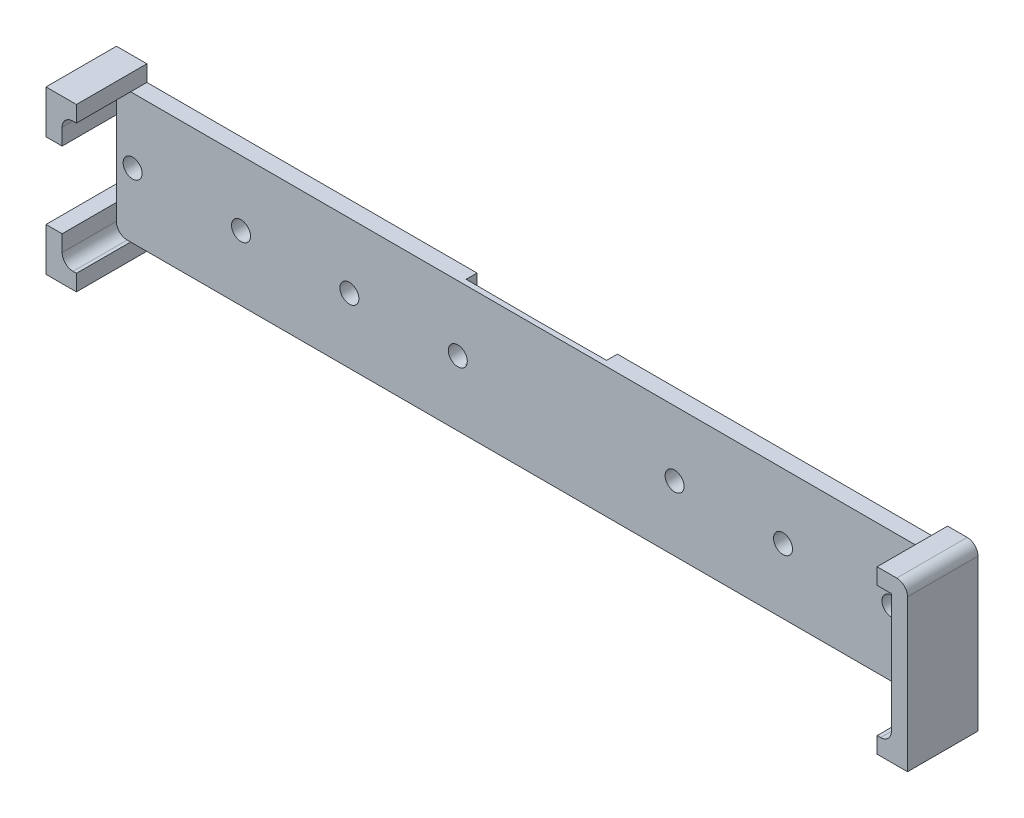
SolidWorks part; units mm, degrees
ref_plane "Front Plane" through (0, 0, 0) normal (0, 0, 1) x (1, 0, 0)
ref_plane "Top Plane" through (0, 0, 0) normal (0, 1, 0) x (1, 0, 0)
ref_plane "Right Plane" through (0, 0, 0) normal (1, 0, 0) x (0, 0, -1)
sketch "Sketch1" plane through (0, 0, 0) normal (0, 0, 1) x (1, 0, 0)
  line L0 (-76.5, 43.2955) -> (-76.5, -49956.7045) construction
  line L1 (-76.5, -12) -> (76.5, -12)
  line L2 (-76.5, -12) -> (-76.5, 12)
  line L3 (-76.5, 12) -> (76.5, 12)
  line L4 (76.5, -12) -> (76.5, 12)
  line L5 (-76.5, -12) -> (76.5, 12) construction
  line L6 (-76.5, 12) -> (76.5, -12) construction
  line L7 (76.5, 42.716) -> (76.5, 17.6033) construction
  point P0 (0, 0)
  dimension "D1" = 153
  dimension "D2" = 24
extrude "Boss-Extrude1" add sketch "Sketch1" along normal blind 3
sketch "Sketch3" plane through (0, 0, 3) normal (0, 0, 1) x (1, 0, 0)
  line L5 (-64.5, 0) -> (938.7663, 0) construction
  line L7 (-79.4776, -9.3658) -> (-79.4776, -12.3658)
  line L8 (-76.5, -9.3658) -> (-76.5, -12)
  line L9 (-70.1258, -5.6258) -> (-82.5217, -18.0217) construction
  line L10 (-76.5, -12) -> (76.5, -12) construction
  line L11 (-73.8658, 14.9776) -> (-73.8658, 12)
  line L12 (-73.8658, -14.9776) -> (-73.8658, -12)
  line L13 (-73.8658, -14.9776) -> (-76.8658, -14.9776)
  line L15 (-73.8658, -12) -> (-76.5, -12)
  line L16 (-79.4776, -12.3658) -> (-79.4776, -14.9776)
  line L17 (-79.4776, -14.9776) -> (-76.8658, -14.9776)
  line L18 (-73.8658, 12) -> (-76.5, 12)
  line L19 (-76.5, 9.3658) -> (-76.5, 12)
  line L21 (-79.4776, 9.3658) -> (-79.4776, 12.3658)
  line L22 (-79.4776, 12.3658) -> (-79.4776, 14.9776)
  line L23 (-79.4776, 14.9776) -> (-76.8658, 14.9776)
  line L24 (-73.8658, 14.9776) -> (-76.8658, 14.9776)
  line L25 (0, 104.9729) -> (0, -49895.0271) construction
  line L42 (-79.4776, 9.3658) -> (-79.4776, 7)
  line L43 (-76.5, 9.3658) -> (-76.5, 7)
  line L44 (-76.5, 12) -> (-76.5, -12) construction
  line L45 (-79.4776, 7) -> (-76.5, 7)
  line L46 (-79.4776, -7) -> (-76.5, -7)
  line L47 (-79.4776, -7) -> (-79.4776, -9.3658)
  line L48 (79.4776, 9.3658) -> (79.4776, -9.3658)
  line L49 (79.4776, -9.3658) -> (79.4776, -12.3658)
  line L50 (79.4776, -12.3658) -> (79.4776, -14.9776)
  line L51 (79.4776, -14.9776) -> (76.8658, -14.9776)
  line L52 (73.8658, -14.9776) -> (76.8658, -14.9776)
  line L53 (73.8658, -14.9776) -> (73.8658, -12)
  line L54 (73.8658, -12) -> (76.5, -12)
  line L55 (76.5, -9.3658) -> (76.5, -12)
  line L56 (76.5, 9.3658) -> (76.5, -9.3658)
  line L57 (76.5, 9.3658) -> (76.5, 12)
  line L58 (73.8658, 12) -> (76.5, 12)
  line L59 (73.8658, 14.9776) -> (73.8658, 12)
  line L60 (73.8658, 14.9776) -> (76.8658, 14.9776)
  line L61 (79.4776, 14.9776) -> (76.8658, 14.9776)
  line L62 (79.4776, 12.3658) -> (79.4776, 14.9776)
  line L63 (79.4776, 9.3658) -> (79.4776, 12.3658)
  line L64 (-76.5, -7) -> (-76.5, -9.3658)
  point P22 (0, -12)
  dimension "D1" = 3
  dimension "D2" = 45
  dimension "D3" = 3
  dimension "D4" = 7
  dimension "D5" = 7
extrude "Boss-Extrude2" add sketch "Sketch3" along normal blind 10 and the other way up to surface (3 mm away) other way up to face at (0, 0, 0)
sketch "Sketch4" plane through (0, -12, 0) normal (0, -1, 0) x (1, 0, 0)
  line L0 (-12.954, 2) -> (-12.954, 0)
  line L1 (0, -6.5532) -> (0, 12.5532) construction
  line L2 (-12.954, 2) -> (0, 2.0683)
  line L3 (-73.8658, 0) -> (73.8658, 0) construction
  line L4 (12.954, 2) -> (0, 2.0683)
  line L5 (12.954, 2) -> (12.954, 0)
  line L6 (-12.954, 0) -> (12.954, 0)
  point P9 (0, 3)
  point P10 (0, 0)
  dimension "D1" = 2
  dimension "D2" = 12.954
extrude "Cut-Extrude1" cut sketch "Sketch4" against normal through all both and the other way through all
sketch "Sketch5" plane through (0, 0, 3) normal (0, 0, 1) x (1, 0, 0)
  line L2 (-76.5, 12) -> (-76.5, 7) construction
  line L3 (-76.5, 7) -> (-76.5, -7) construction
  circle A0 centre (-73.5, 0) radius 1.75
  point P6 (-74.5, 9.5)
  point P8 (-74.5, 9.5)
  point P11 (-76.5, 0)
  dimension "D1" = 3.5
  dimension "D2" = 3
extrude "Cut-Extrude2" cut sketch "Sketch5" against normal through all both and the other way through all
fillet "Fillet1" radius 2 4 edges at (79.4776, 14.9776, 6.5) (-76.5, 12, 8) (-76.5, -12, 8) (76.5, -12, 8)
pattern_linear "LPattern1" count 8 spacing 20 along (1, 0, 0) skipping (4, 0) of "Cut-Extrude2"
